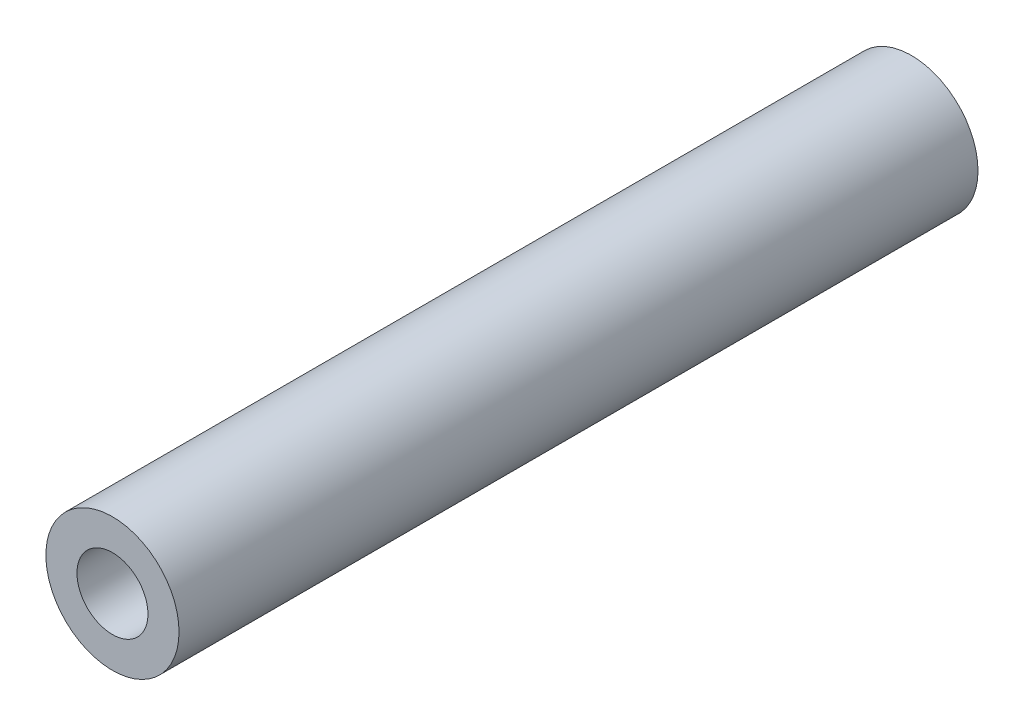
SolidWorks part; units mm, degrees
ref_plane "正面" through (0, 0, 0) normal (0, 0, 1) x (1, 0, 0)
ref_plane "平面" through (0, 0, 0) normal (0, 1, 0) x (1, 0, 0)
ref_plane "右側面" through (0, 0, 0) normal (1, 0, 0) x (0, 0, -1)
sketch "ｽｹｯﾁ1" plane through (0, 0, 0) normal (0, 0, 1) x (1, 0, 0)
  circle A0 centre (0, 0) radius 3
  dimension "D1" = 6
extrude "ﾎﾞｽ - 押し出し1" add sketch "ｽｹｯﾁ1" along normal blind 36
sketch "ｽｹｯﾁ2" plane through (0, 0, 36) normal (0, 0, 1) x (1, 0, 0)
  circle A0 centre (0, 0) radius 1.6
  dimension "D1" = 3.2
extrude "ｶｯﾄ - 押し出し1" cut sketch "ｽｹｯﾁ2" against normal blind 36
